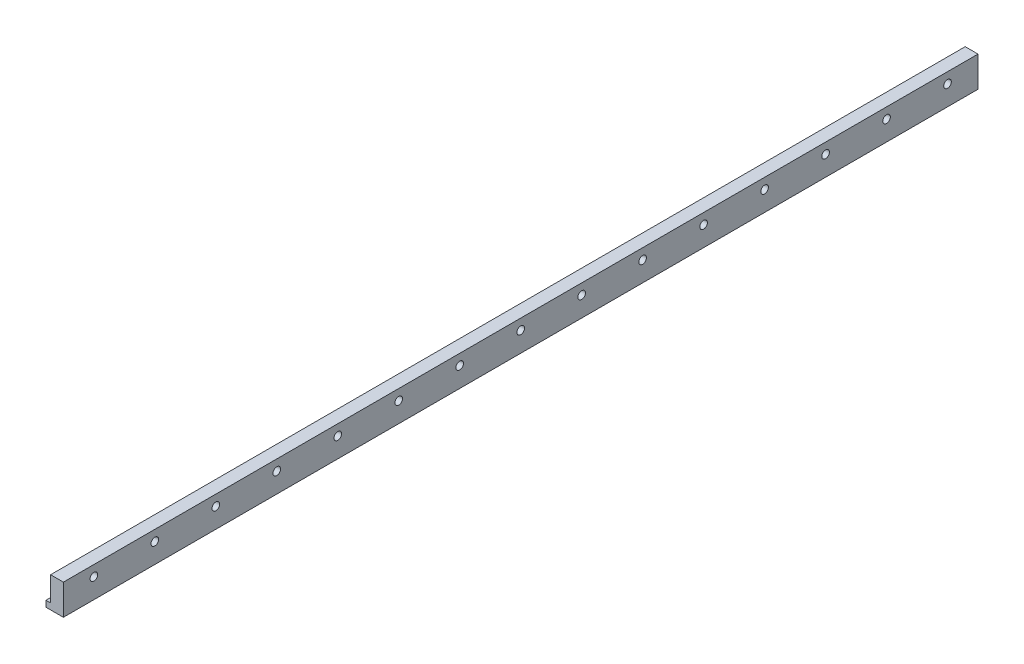
SolidWorks part; units mm, degrees
ref_plane "Front Plane" through (0, 0, 0) normal (0, 0, 1) x (1, 0, 0)
ref_plane "Top Plane" through (0, 0, 0) normal (0, 1, 0) x (1, 0, 0)
ref_plane "Right Plane" through (0, 0, 0) normal (1, 0, 0) x (0, 0, -1)
sketch "Sketch1" plane through (0, 0, 0) normal (0, 0, 1) x (1, 0, 0)
  line L1 (2.1, 4.525) -> (-2.1, 4.525)
  line L2 (2.1, 4.525) -> (2.1, -4.525)
  line L3 (2.1, -4.525) -> (-2.1, -4.525)
  line L4 (-2.1, 4.525) -> (-2.1, -4.525)
  line L5 (0, -4.525) -> (0, 4.525) construction
  line L6 (2.1, 0) -> (-2.1, 0) construction
  point P0 (0, 0)
  dimension "D1" = 4.2
  dimension "D2" = 9.05
extrude "Boss-Extrude1" add sketch "Sketch1" along normal mid plane 300
hole_wizard "M3x0.5 Tapped Hole1" positions "Sketch5" profile "Sketch6" tap size "M3x0.5" standard "ANSI Metric" end condition through all
sketch "Sketch5" plane through (-2.1, 0, 0) normal (-1, 0, 0) x (0, 0, 1)
  line L0 (-150, 0) -> (-140, 0) construction
  line L1 (-150, 4.525) -> (-150, -4.525) construction
  point P0 (-140, 0)
  dimension "D1" = 10
sketch "Sketch6" plane through (-2.1, 0, -140) normal (0, 1, 0) x (0, 0, 1)
  line L0 (0, 0) -> (0, 4.2)
  line L1 (0, 4.2) -> (1.25, 4.2)
  line L2 (1.25, 4.2) -> (1.25, 0)
  line L5 (1.25, 0) -> (0, 0)
  line L11 (0, -6.35) -> (0, 107.95) construction
  dimension "Thru Tap Drill Dia." = 2.5
  dimension "Thru Tap Drill Depth" = 4.2
pattern_linear "LPattern1" count 15 spacing 20 along (0, 0, 1) of "M3x0.5 Tapped Hole1"
sketch "Sketch7" plane through (0, 0, 150) normal (0, 0, 1) x (1, 0, 0)
  line L0 (-2.1, 4.525) -> (-2.1, -4.525) construction
  line L1 (2.1, 4.525) -> (-3.6, 4.525)
  line L2 (2.1, 4.525) -> (2.1, 6.525)
  line L3 (2.1, 6.525) -> (-3.6, 6.525)
  line L4 (-3.6, 4.525) -> (-3.6, 6.525)
  line L5 (-0.75, 6.525) -> (-0.75, 4.525) construction
  line L6 (2.1, 5.525) -> (-3.6, 5.525) construction
  line L7 (2.1, -4.525) -> (-3.6, -4.525)
  line L8 (2.1, -4.525) -> (2.1, -6.525)
  line L9 (2.1, -6.525) -> (-3.6, -6.525)
  line L10 (-3.6, -4.525) -> (-3.6, -6.525)
  line L11 (-0.75, -6.525) -> (-0.75, -4.525) construction
  line L12 (2.1, -5.525) -> (-3.6, -5.525) construction
  point P268 (-0.75, -5.525)
  point P476 (-0.75, 5.525)
  dimension "D1" = 1.5
  dimension "D2" = 2
extrude "Boss-Extrude3" add sketch "Sketch7" against normal up to surface (300 mm away) up to face at (0, 0, -150)
sketch "Sketch8" plane through (2.1, 0, 0) normal (1, 0, 0) x (0, 0, -1)
  line L0 (150, -6.525) -> (-150, -6.525) construction
  line L1 (-150, 6.525) -> (-130, 6.525)
  line L2 (-150, 6.525) -> (-150, -6.525)
  line L3 (-150, -6.525) -> (-130, -6.525)
  line L4 (-130, 6.525) -> (-130, -6.525)
  line L5 (-140, -6.525) -> (-140, 6.525) construction
  line L6 (-150, 0) -> (-130, 0) construction
  line L8 (150, 6.525) -> (130, 6.525)
  line L9 (150, 6.525) -> (150, -6.525)
  line L10 (150, -6.525) -> (130, -6.525)
  line L11 (130, 6.525) -> (130, -6.525)
  line L12 (140, -6.525) -> (140, 6.525) construction
  line L13 (150, 0) -> (130, 0) construction
  circle A0 centre (120, 0) radius 1.25 construction
  point P78 (140, 0)
  point P188 (-140, 0)
  dimension "D1" = 10
extrude "Cut-Extrude1" [suppressed] cut sketch "Sketch8" against normal through all
sketch "Sketch9" plane through (0, 0, 150) normal (0, 0, 1) x (1, 0, 0)
  line L1 (2.1, 6.525) -> (-3.6, 6.525)
  line L2 (2.1, 6.525) -> (2.1, 3.475)
  line L3 (2.1, 3.475) -> (-3.6, 3.475)
  line L4 (-3.6, 6.525) -> (-3.6, 3.475)
  line L5 (-0.75, 3.475) -> (-0.75, 6.525) construction
  line L6 (2.1, 5) -> (-3.6, 5) construction
  line L9 (-2.1, -4.525) -> (-3.6, -4.525) construction
  point P4 (-3.6, -6.525)
  point P5 (2.1, 6.525)
  point P6 (-3.6, 6.525)
  point P236 (-0.75, 5)
  dimension "D1" = 8
extrude "Cut-Extrude2" cut sketch "Sketch9" against normal through all
